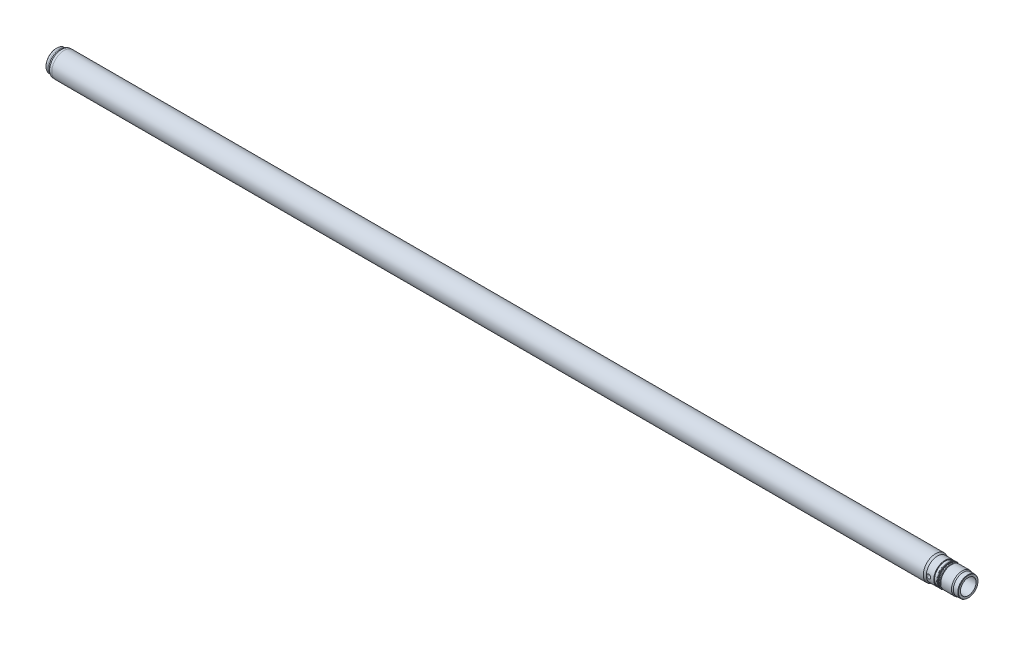
SolidWorks part; units mm, degrees
ref_plane "Front" through (0, 0, 0) normal (0, 0, 1) x (1, 0, 0)
ref_plane "Top" through (0, 0, 0) normal (0, 1, 0) x (1, 0, 0)
ref_plane "Right" through (0, 0, 0) normal (1, 0, 0) x (0, 0, -1)
sketch "Sketch1" plane through (0, 0, 0) normal (0, 0, 1) x (1, 0, 0)
  line L0 (0, 0) -> (2045, 0) construction
  line L1 (0, 21) -> (0, 23.5)
  line L2 (0.5, 24) -> (5, 24)
  line L3 (5, 24) -> (5, 24.75)
  line L4 (11.8301, 27.25) -> (17, 27.25)
  line L5 (17, 27.25) -> (17, 27.5)
  line L6 (5, 24.75) -> (7.5, 24.75)
  line L7 (7.5, 24.75) -> (11.8301, 27.25)
  line L8 (17, 27.5) -> (1971.6699, 27.5)
  line L9 (0, 21) -> (6.0622, 17.5)
  line L10 (6.0622, 17.5) -> (2045, 17.5)
  line L11 (1993, 24.5) -> (1993, 23.5)
  line L12 (1976, 25) -> (1992.5, 25)
  line L13 (1993, 23.5) -> (1999, 23.5)
  line L14 (1999, 23.5) -> (1999, 24.5)
  line L15 (1999.5, 25) -> (2001, 25)
  line L16 (1976, 25) -> (1971.6699, 27.5)
  line L17 (2001, 25) -> (2002, 24.4226)
  line L18 (2002, 24.4226) -> (2002, 23.75)
  line L19 (2003, 22.75) -> (2005, 22.75)
  line L20 (2005, 22.75) -> (2007.4533, 24)
  line L21 (2007.4533, 24) -> (2031.4019, 24)
  line L22 (2045, 21.9226) -> (2045, 17.5)
  line L23 (0.5, 24) -> (0, 23.5)
  line L24 (2031.4019, 24) -> (2034, 22.5)
  line L25 (2034, 22.5) -> (2044, 22.5)
  line L26 (2044, 22.5) -> (2045, 21.9226)
  arc A0 (1992.5, 25) -> (1993, 24.5) centre (1992.5, 24.5) cw
  arc A1 (1999, 24.5) -> (1999.5, 25) centre (1999.5, 24.5) cw
  arc A2 (2002, 23.75) -> (2003, 22.75) centre (2003, 23.75) ccw
  dimension "D35" = 0.5
  dimension "D36" = 1
  dimension "D3" = 5
  dimension "D4" = 48
  dimension "D5" = 1
  dimension "D6" = 46
  dimension "D7" = 30
  dimension "D8" = 7.5
  dimension "D9" = 35
  dimension "D10" = 30
  dimension "D11" = 42
  dimension "D12" = 48
  dimension "D13" = 45.5
  dimension "D14" = 27
  dimension "D15" = 69
  dimension "D16" = 30
  dimension "D17" = 6
  dimension "D18" = 43
  dimension "D19" = 3
  dimension "D20" = 47
  dimension "D21" = 2045
  dimension "D22" = 50
  dimension "D23" = 55
  dimension "D24" = 49.5
  dimension "D25" = 0.5
  dimension "D26" = 45
  dimension "D27" = 17
  dimension "D28" = 54.5
  dimension "D29" = 30
  dimension "D30" = 45
  dimension "D31" = 11
  dimension "D32" = 30
  dimension "D33" = 30
  dimension "D34" = 1
revolve "Base-Revolve" add sketch "Sketch1" angle 360 about L0
cosmetic thread "Cosmetic Thread1" parameters "D2"=45.835
sketch "Sketch2" plane through (0, 0, 0) normal (0, 0, 1) x (1, 0, 0)
  line L0 (0, 0) -> (2045, 0) construction
  line L4 (2045, -22.5) -> (2045, 22.5) construction
  circle A0 centre (1981, 0) radius 4.5
  dimension "D2" = 9
  dimension "D1" = 64
extrude "ø9 gennemgående hul" cut sketch "Sketch2" against normal mid plane 100
